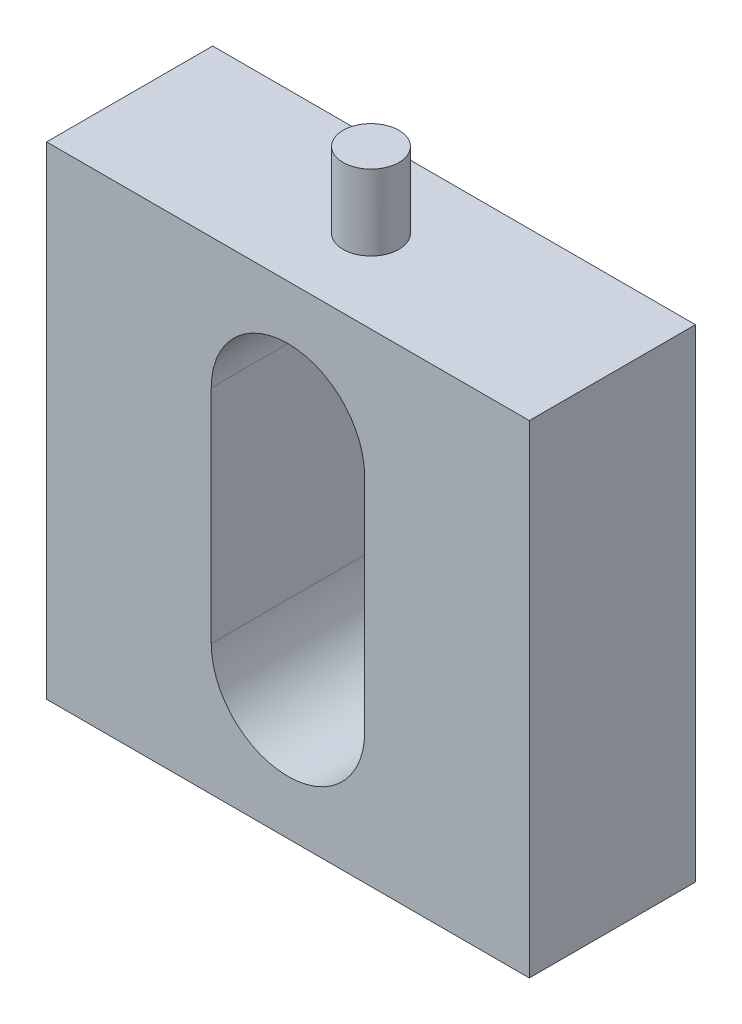
SolidWorks part; units mm, degrees
ref_plane "Front Plane" through (0, 0, 0) normal (0, 0, 1) x (1, 0, 0)
ref_plane "Top Plane" through (0, 0, 0) normal (0, 1, 0) x (1, 0, 0)
ref_plane "Right Plane" through (0, 0, 0) normal (1, 0, 0) x (0, 0, -1)
sketch "Sketch1" plane through (0, 0, 0) normal (0, 0, 1) x (1, 0, 0)
  line L1 (0, 0) -> (13.843, 0)
  line L2 (0, 0) -> (0, -13.843)
  line L3 (0, -13.843) -> (13.843, -13.843)
  line L4 (13.843, 0) -> (13.843, -13.843)
  dimension "D1" = 13.843
  dimension "D2" = 13.843
extrude "Boss-Extrude1" add sketch "Sketch1" along normal blind 4.7625
sketch "Sketch2" plane through (0, 0, 0) normal (0, 1, 0) x (1, 0, 0)
  line L0 (0, -4.7625) -> (0, 0) construction
  line L1 (13.843, 0) -> (0, 0) construction
  circle A0 centre (6.9215, -2.3813) radius 0.8001
  point P2 (0, 0)
  point P5 (0, -2.3813)
  point P6 (0, 0)
  point P9 (6.9215, 0)
  dimension "D1" = 1.6002
extrude "Boss-Extrude2" add sketch "Sketch2" along normal blind 2.159
sketch "Sketch3" plane through (0, 0, 0) normal (0, 0, -1) x (-1, 0, 0)
  line L0 (0, -13.843) -> (-13.843, -13.843) construction
  line L1 (0, 0) -> (0, -13.843) construction
  line L2 (-9.1215, -10.0965) -> (-9.1215, -3.7465)
  line L3 (-4.7215, -10.0965) -> (-4.7215, -3.7465)
  arc A1 (-9.1215, -3.7465) -> (-4.7215, -3.7465) centre (-6.9215, -3.7465) cw
  arc A2 (-9.1215, -10.0965) -> (-4.7215, -10.0965) centre (-6.9215, -10.0965) ccw
  point P0 (0, 0)
  point P1 (-6.9215, -1.5465)
  point P5 (-6.9215, -13.843)
  point P9 (0, -6.9215)
  point P11 (-9.1215, -6.9215)
  point P14 (-4.7215, -6.9215)
  dimension "D1" = 4.4
  dimension "D3" = 2.2
  dimension "D2" = 6.35
extrude "Cut-Extrude1" cut sketch "Sketch3" against normal blind 8.001
